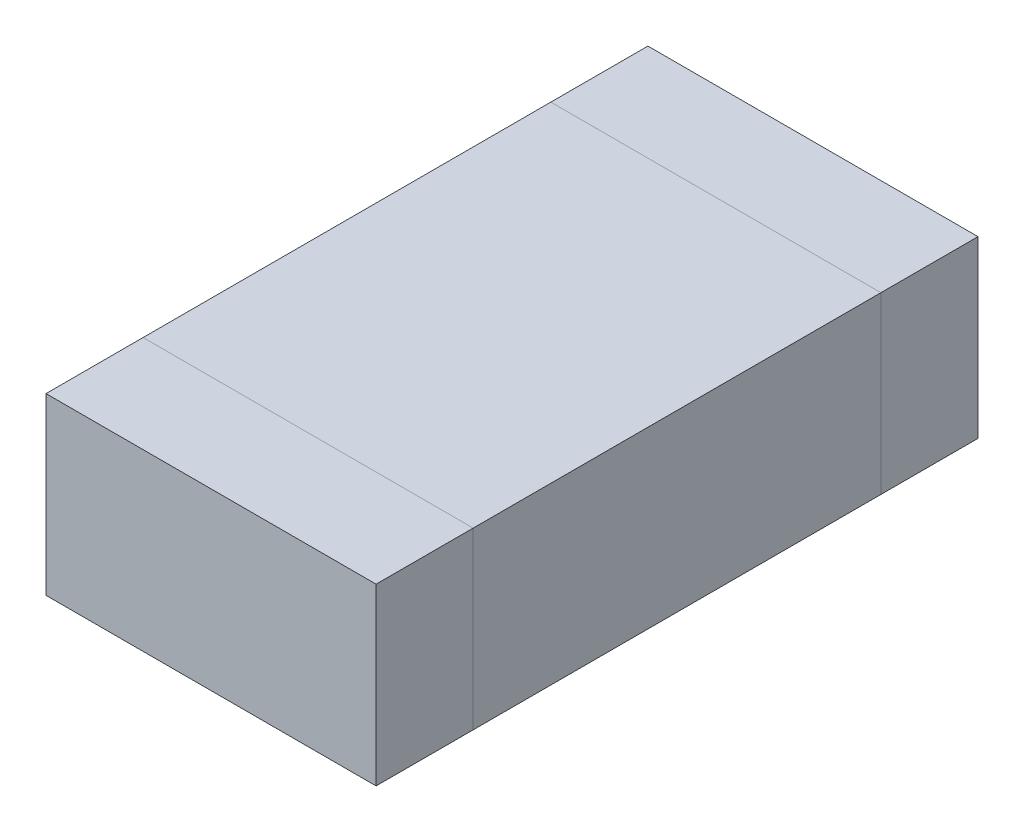
SolidWorks part; units mm, degrees
ref_plane "Front Plane" through (0, 0, 0) normal (0, 0, 1) x (1, 0, 0)
ref_plane "Top Plane" through (0, 0, 0) normal (0, 1, 0) x (1, 0, 0)
ref_plane "Right Plane" through (0, 0, 0) normal (1, 0, 0) x (0, 0, -1)
sketch "MainBodyS" plane through (0, 0, 0) normal (0, 1, 0) x (1, 0, 0)
  line L1 (-0.425, 0.525) -> (0.425, 0.525)
  line L2 (-0.425, 0.525) -> (-0.425, -0.525)
  line L3 (-0.425, -0.525) -> (0.425, -0.525)
  line L4 (0.425, 0.525) -> (0.425, -0.525)
  line L5 (-0.425, 0.525) -> (0.425, -0.525) construction
  line L6 (-0.425, -0.525) -> (0.425, 0.525) construction
  point P0 (0, 0)
  dimension "Length" = 1.05
  dimension "Width" = 0.85
extrude "MainBody" add sketch "MainBodyS" along normal blind 0.45
sketch "LeftBodyS" plane through (0, 0, 0) normal (0, -1, 0) x (-1, 0, 0)
  line L1 (0.425, -0.525) -> (-0.425, -0.525)
  line L2 (0.425, -0.525) -> (0.425, -0.775)
  line L3 (0.425, -0.775) -> (-0.425, -0.775)
  line L4 (-0.425, -0.525) -> (-0.425, -0.775)
  dimension "SolderLength" = 0.25
extrude "LeftBody" add sketch "LeftBodyS" against normal up to surface (0.45 mm away) separate body up to face at (0, 0.45, 0)
sketch "RightBodyS" plane through (0, 0, 0) normal (0, -1, 0) x (1, 0, 0)
  line L0 (0.425, 0.525) -> (0.425, 0.775) construction
  line L1 (-0.425, -0.525) -> (0.425, -0.525)
  line L2 (-0.425, -0.525) -> (-0.425, -0.775)
  line L3 (-0.425, -0.775) -> (0.425, -0.775)
  line L4 (0.425, -0.525) -> (0.425, -0.775)
extrude "RightBody" add sketch "RightBodyS" against normal up to surface (0.45 mm away) separate body up to face at (0, 0.45, 0)
